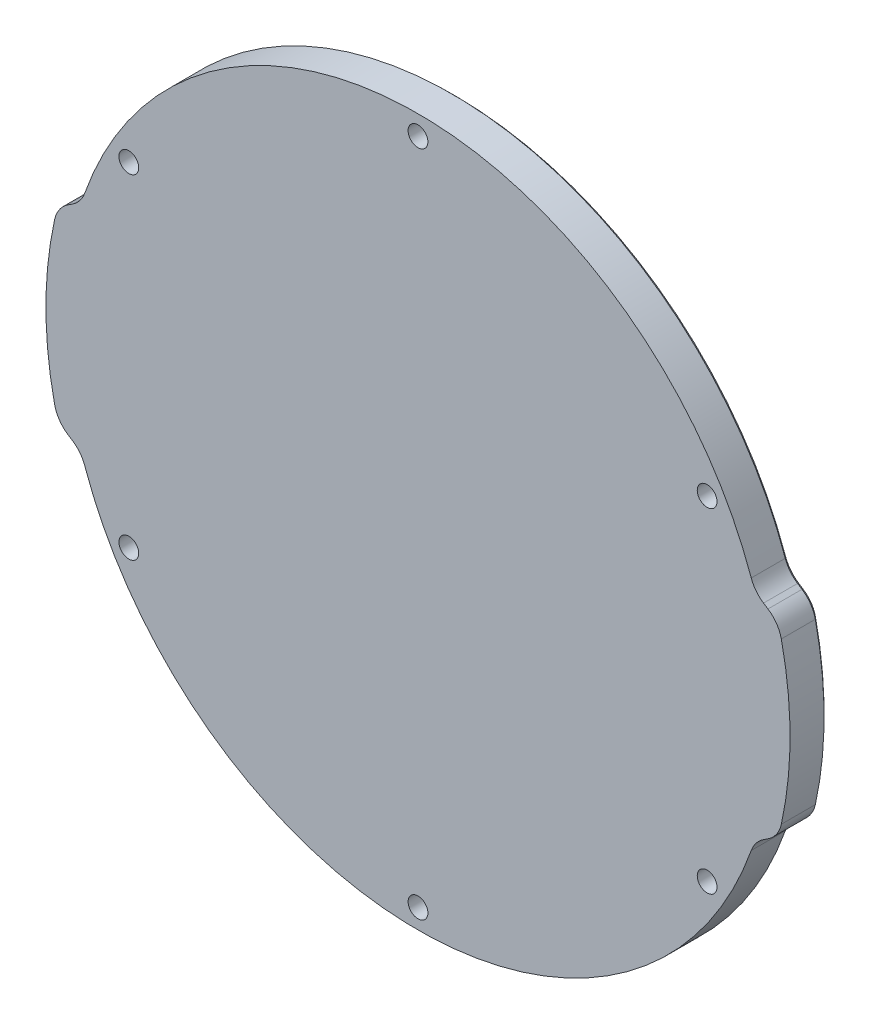
SolidWorks part; units mm, degrees
ref_plane "前视基准面" through (0, 0, 0) normal (0, 0, 1) x (1, 0, 0)
ref_plane "上视基准面" through (0, 0, 0) normal (0, 1, 0) x (1, 0, 0)
ref_plane "右视基准面" through (0, 0, 0) normal (1, 0, 0) x (0, 0, -1)
ref_plane "基准面4" through (0, 0, 6) normal (0, 0, 1) x (1, 0, 0)
sketch "草图1" plane through (0, 0, 6) normal (0, 0, 1) x (1, 0, 0)
  line L0 (-54.4047, 17.5) -> (-58.2497, 15)
  line L1 (58.2497, 15) -> (54.4047, 17.5)
  arc A0 (-58.2497, 15) -> (58.2497, 15) centre (0, 0) ccw
  arc A1 (54.4047, 17.5) -> (-54.4047, 17.5) centre (0, 0) ccw
extrude "凸台-拉伸1" add sketch "草图1" against normal blind 6
sketch "草图2" plane through (0, 0, 0) normal (0, 0, -1) x (-1, 0, 0)
  line L0 (58.2497, -15) -> (54.4047, -17.5)
  line L1 (-54.4047, -17.5) -> (-58.2497, -15)
  arc A0 (54.4047, -17.5) -> (-54.4047, -17.5) centre (0, 0) cw
  arc A1 (-58.2497, -15) -> (58.2497, -15) centre (0, 0) ccw
extrude "切除-拉伸1" cut sketch "草图2" against normal through all
hole_wizard "Ø3.2 (3.2) 直径孔1" positions "草图4" profile "草图3" hole size "Ø3.2" standard "ANSI Metric"
sketch "草图4" plane through (0, 0, 0) normal (0, 0, -1) x (-1, 0, 0)
  point P0 (0, 53.975)
  point P1 (46.7437, -26.9875)
  point P2 (-46.7437, 26.9875)
  point P3 (-46.7437, -26.9875)
  point P4 (0, -53.975)
  point P5 (46.7437, 26.9875)
sketch "草图3" plane through (0, 53.975, 0) normal (1, 0, 0) x (0, 1, 0)
  line L0 (0, 0) -> (0, 6)
  line L1 (0, 6) -> (1.6, 6)
  line L2 (1.6, 6) -> (1.6, 0)
  line L5 (1.6, 0) -> (0, 0)
  line L11 (0, -6.35) -> (0, 107.95) construction
  dimension "通孔孔直径" = 3.2
  dimension "通孔孔深度" = 6
fillet "圆角1" radius 5 8 edges at (-54.4047, -17.5, 3) (58.2497, 15, 3) (54.4047, -17.5, 3) (-58.2497, -15, 3) (54.4047, 17.5, 3) (-54.4047, 17.5, 3) (58.2497, -15, 3) (-58.2497, 15, 3)
chamfer "倒角1" distance 0.5 angle 45 16 edges at (0, 57.15, 0) (54.6578, 17.6514, 0) (-54.6578, 17.6514, 0) (56.2186, 16.3206, 0) (-56.2186, 16.3206, 0) (57.962, 14.7428, 0) (-57.962, 14.7428, 0) (60.15, 0, 0) (-60.15, 0, 0) (57.962, -14.7428, 0) (-57.962, -14.7428, 0) (56.2186, -16.3206, 0) (-56.2186, -16.3206, 0) (54.6578, -17.6514, 0) (-54.6578, -17.6514, 0) (0, -57.15, 0)
